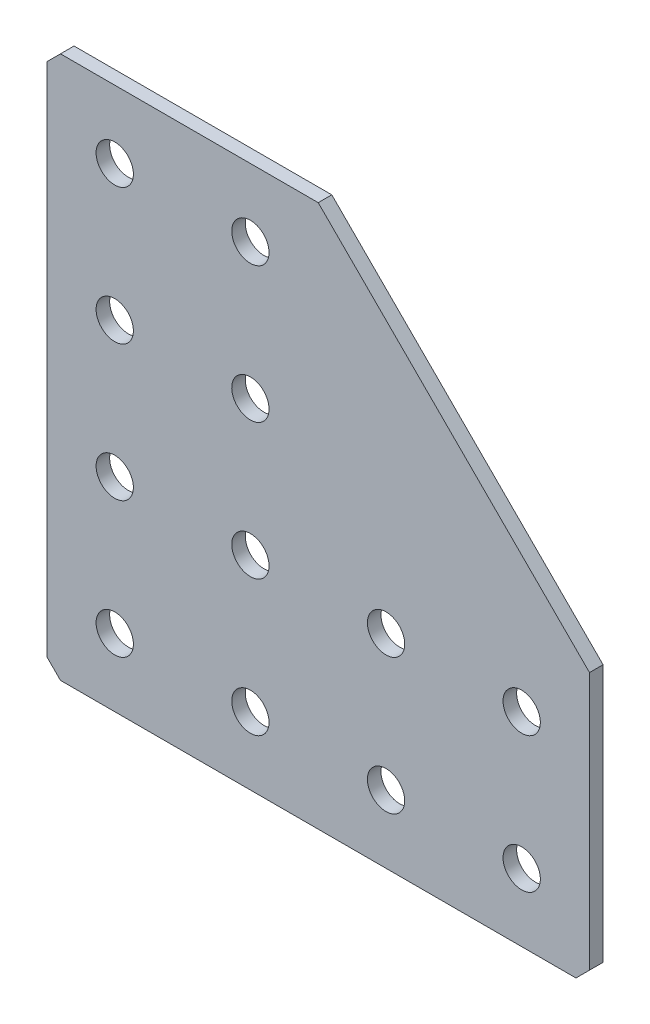
SolidWorks part; units mm, degrees
material "Простая углеродистая сталь"
ref_plane "Спереди(Плоскость XY)" through (0, 0, 0) normal (0, 0, 1) x (1, 0, 0)
ref_plane "Сверху(Плоскость XZ)" through (0, 0, 0) normal (0, 1, 0) x (1, 0, 0)
ref_plane "Справа(Плоскость ZY)" through (0, 0, 0) normal (1, 0, 0) x (0, 0, -1)
sketch "Эскиз1" plane through (0, 0, 0) normal (0, 0, -1) x (1, 0, 0)
  line L0 (0, 0) -> (0, 80)
  line L1 (0, 80) -> (80, 80)
  line L2 (80, 80) -> (80, 40)
  line L3 (80, 40) -> (40, 40) construction
  line L4 (40, 40) -> (40, 0) construction
  line L5 (40, 0) -> (0, 0)
  line L6 (80, 40) -> (40, 0)
  dimension "D1" = 80
  dimension "D2" = 40
  dimension "D3" = 40
  dimension "D4" = 80
extrude "Бобышка-Вытянуть1" add sketch "Эскиз1" along normal blind 2
hole_wizard "Отверстие с зазором M51" positions "Эскиз2" profile "Эскиз3" hole size "M5" standard "DIN" end condition through all
sketch "Эскиз2" plane through (0, 0, -2) normal (0, 0, -1) x (1, 0, 0)
  line L0 (10, 0) -> (10, 80) construction
  line L1 (0, 0) -> (40, 0) construction
  line L2 (80, 80) -> (0, 80) construction
  line L3 (0, 80) -> (0, 0) construction
  line L4 (0, 0) -> (40, 0) construction
  point P0 (10, 70)
  point P2 (10, 50)
  point P4 (10, 30)
  point P6 (10, 10)
  point P27 (30, 70)
  point P29 (30, 50)
  point P35 (30, 30)
  point P37 (30, 10)
  point P39 (50, 70)
  point P41 (50, 50)
  point P53 (70, 70)
  point P55 (70, 50)
  dimension "D1" = 20
  dimension "D2" = 20
  dimension "D3" = 20
  dimension "D4" = 10
  dimension "D5" = 20
  dimension "D6" = 10
  dimension "D7" = 20
  dimension "D8" = 20
sketch "Эскиз3" plane through (10, -70, -2) normal (1, 0, 0) x (0, 1, 0)
  line L0 (0, 0) -> (0, 2)
  line L1 (0, 2) -> (2.75, 2)
  line L2 (2.75, 2) -> (2.75, 0)
  line L5 (2.75, 0) -> (0, 0)
  line L11 (0, -6.35) -> (0, 107.95) construction
  dimension "Диаметр сквозного отверстия" = 5.5
  dimension "Глубина сквозного отверстия" = 2
chamfer "Фаска1" distance 2 angle 45 3 edges at (0, 0, -1) (80, -80, -1) (0, -80, -1)
